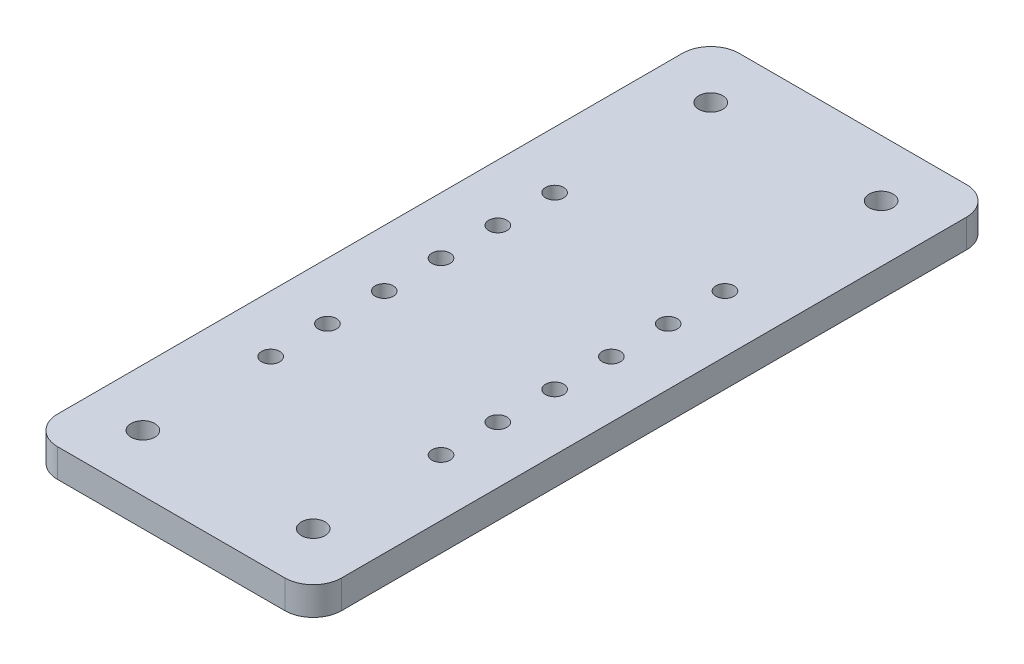
SolidWorks part; units mm, degrees
ref_plane "Front Plane" through (0, 0, 0) normal (0, 0, 1) x (1, 0, 0)
ref_plane "Top Plane" through (0, 0, 0) normal (0, 1, 0) x (1, 0, 0)
ref_plane "Right Plane" through (0, 0, 0) normal (1, 0, 0) x (0, 0, -1)
sketch "Sketch1" plane through (0, 0, 0) normal (0, 1, 0) x (1, 0, 0)
  line L1 (-25, 40) -> (25, 40)
  line L2 (-25, 40) -> (-25, -40)
  line L3 (-25, -40) -> (25, -40)
  line L4 (25, 40) -> (25, -40)
  line L5 (0, -40) -> (0, 40) construction
  line L6 (-25, 0) -> (25, 0) construction
  line L7 (-25, -40) -> (25, -40)
  line L8 (-25, -40) -> (-25, -60)
  line L9 (-25, -60) -> (25, -60)
  line L10 (25, -40) -> (25, -60)
  line L11 (0, -60) -> (0, -40) construction
  line L12 (-25, -50) -> (25, -50) construction
  line L13 (-15, -40) -> (15, -40) construction
  line L14 (-15, -40) -> (-15, 12.5) construction
  line L15 (-15, 12.5) -> (15, 12.5) construction
  line L16 (15, -40) -> (15, 12.5) construction
  line L17 (0, 12.5) -> (0, -40) construction
  line L18 (-15, -13.75) -> (15, -13.75) construction
  line L19 (-15, 22.5) -> (15, 22.5) construction
  line L20 (-15, 22.5) -> (-15, 2.5) construction
  line L21 (-15, 2.5) -> (15, 2.5) construction
  line L22 (15, 22.5) -> (15, 2.5) construction
  line L23 (0, 2.5) -> (0, 22.5) construction
  line L24 (-15, 12.5) -> (15, 12.5) construction
  line L25 (25, 40) -> (-25, 40)
  line L26 (25, 40) -> (25, 60)
  line L27 (25, 60) -> (-25, 60)
  line L28 (-25, 40) -> (-25, 60)
  line L29 (0, 60) -> (0, 40) construction
  line L30 (25, 50) -> (-25, 50) construction
  circle A0 centre (-15, -50) radius 2.1
  circle A1 centre (15, -50) radius 2.1
  circle A2 centre (-15, 22.5) radius 1.6
  circle A3 centre (15, 22.5) radius 1.6
  circle A4 centre (-15, 12.5) radius 1.6
  circle A5 centre (15, 12.5) radius 1.6
  circle A6 centre (-15, 2.5) radius 1.6
  circle A7 centre (15, 2.5) radius 1.6
  circle A8 centre (-15, -7.5) radius 1.6
  circle A9 centre (15, -7.5) radius 1.6
  circle A10 centre (-15, -17.5) radius 1.6
  circle A11 centre (15, -17.5) radius 1.6
  circle A12 centre (-15, -27.5) radius 1.6
  circle A13 centre (15, -27.5) radius 1.6
  circle A14 centre (15, 50) radius 2.1
  circle A15 centre (-15, 50) radius 2.1
  point P0 (0, 0)
  point P117 (0, -13.75)
  point P136 (0, -50)
  point P271 (0, 50)
  dimension "D4" = 4.2
  dimension "D9" = 3.2
  dimension "D11" = 20
  dimension "D12" = 4.2
  dimension "D1" = 80
  dimension "D2" = 50
  dimension "D3" = 20
  dimension "D5" = 30
  dimension "D6" = 52.5
  dimension "D7" = 30
  dimension "D8" = 20
  dimension "D13" = 30
  dimension "D10" = 6
extrude "Boss-Extrude1" add sketch "Sketch1" along normal blind 5 contours L4 L1 L2 L3 A13 A12 A11 A10 A9 A8 A7 A6 A5 A4 A3 A2 | L10 L3 L8 L9 A0 A1 | L26 L25 L28 L27 | A14 | A15
fillet "Fillet2" radius 5 4 edges at (-25, 2.5, 60) (25, 2.5, 60) (25, 2.5, -60) (-25, 2.5, -60)
